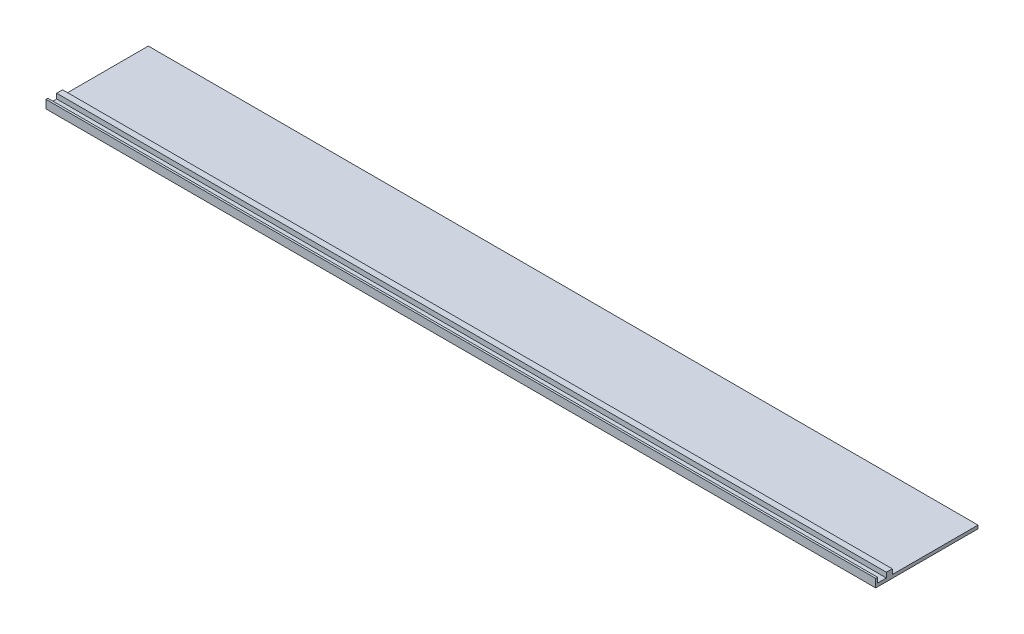
SolidWorks part; units mm, degrees
ref_plane "Спереди" through (0, 0, 0) normal (0, 0, 1) x (1, 0, 0)
ref_plane "Сверху" through (0, 0, 0) normal (0, 1, 0) x (1, 0, 0)
ref_plane "Справа" through (0, 0, 0) normal (1, 0, 0) x (0, 0, -1)
sketch "Эскиз1" plane through (0, 0, 0) normal (1, 0, 0) x (0, 0, -1)
  line L0 (-92.5, 0) -> (92.5, 0)
  line L1 (-92.5, 0) -> (-92.5, 15)
  line L2 (-92.5, 15) -> (-88.9887, 15)
  line L3 (-88.9887, 15) -> (-88.9887, 6)
  line L4 (-88.9887, 6) -> (-73.248, 6)
  line L5 (-73.248, 6) -> (-73.248, 15)
  line L6 (-73.248, 15) -> (-62.5157, 15)
  line L7 (-62.5157, 15) -> (-62.5157, 6)
  line L8 (-62.5157, 6) -> (92.5, 6)
  line L9 (92.5, 6) -> (92.5, 0)
  point P10 (0, 0)
extrude "Бобышка-Вытянуть1" add sketch "Эскиз1" along normal blind 1500
